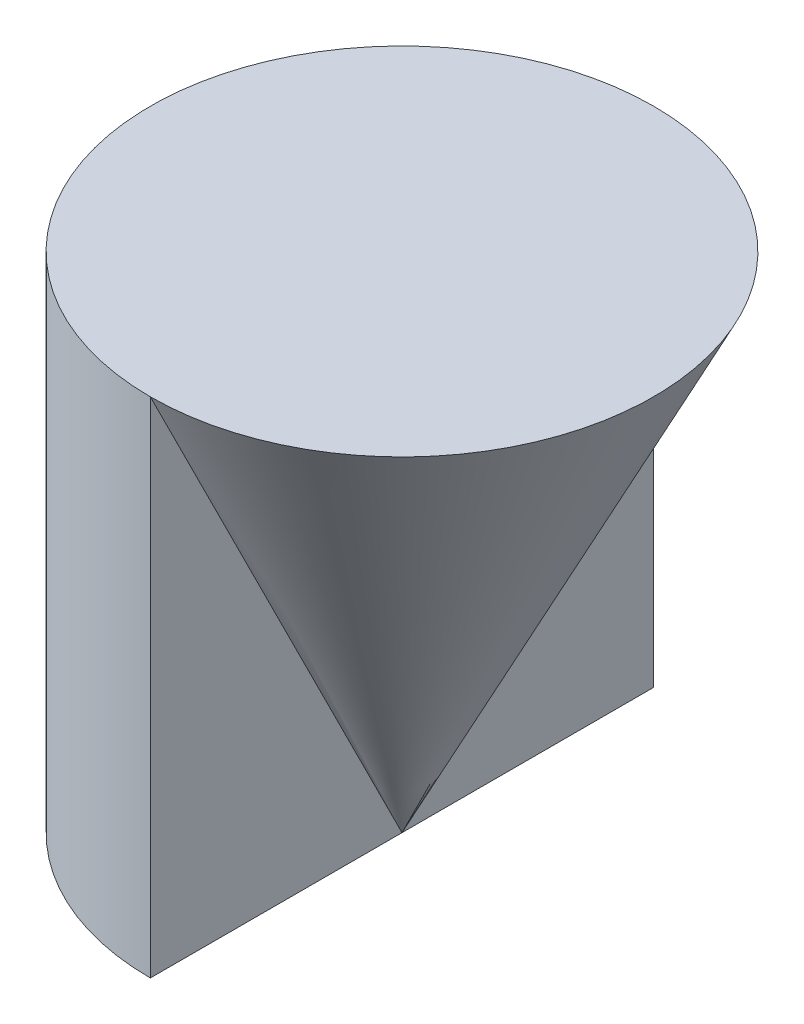
SolidWorks part; units mm, degrees
ref_plane "Front" through (0, 0, 0) normal (0, 0, 1) x (1, 0, 0)
ref_plane "Top" through (0, 0, 0) normal (0, 1, 0) x (1, 0, 0)
ref_plane "Right" through (0, 0, 0) normal (1, 0, 0) x (0, 0, -1)
sketch "Sketch1" plane through (0, 0, 0) normal (0, 1, 0) x (1, 0, 0)
  line L0 (0, 2) -> (0, -2)
  arc A0 (0, 2) -> (0, -2) centre (0, 0) ccw
  dimension "D2" = 2
  dimension "D1" = 2
extrude "Boss-Extrude1" add sketch "Sketch1" along normal blind 4
sketch "Sketch2" plane through (0, 0, 0) normal (1, 0, 0) x (0, 0, -1)
  line L0 (0, 0) -> (2, 4)
  line L1 (2, 4) -> (0, 4)
  line L2 (-2, 4) -> (2, 4) construction
  line L3 (0, 4) -> (0, 0)
revolve "Revolve1" add sketch "Sketch2" angle 180 about L3
